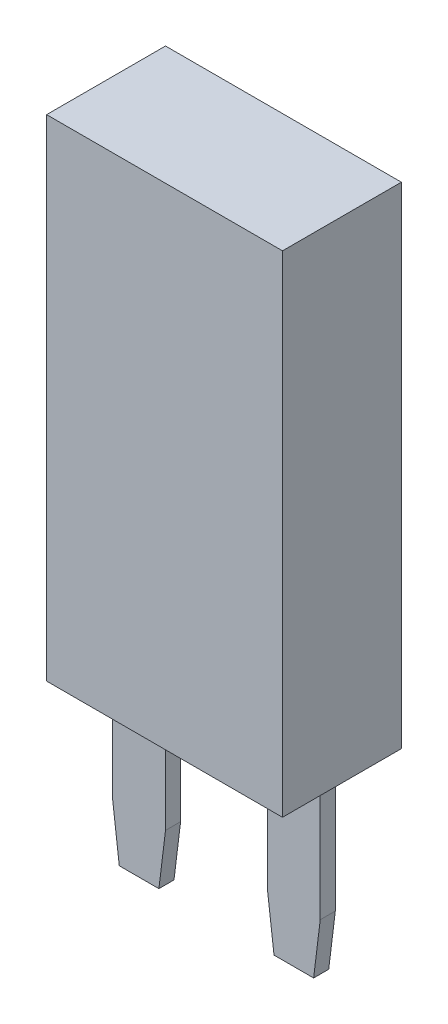
SolidWorks part; units mm, degrees
ref_plane "Front Plane" through (0, 0, 0) normal (0, 0, 1) x (1, 0, 0)
ref_plane "Top Plane" through (0, 0, 0) normal (0, 1, 0) x (1, 0, 0)
ref_plane "Right Plane" through (0, 0, 0) normal (1, 0, 0) x (0, 0, -1)
sketch "Sketch1" plane through (0, 0, 0) normal (0, 0, 1) x (1, 0, 0)
  line L1 (-6.25, 13) -> (6.25, 13)
  line L2 (-6.25, 13) -> (-6.25, -13)
  line L3 (-6.25, -13) -> (6.25, -13)
  line L4 (6.25, 13) -> (6.25, -13)
  line L5 (-6.25, 13) -> (6.25, -13) construction
  line L6 (-6.25, -13) -> (6.25, 13) construction
  point P0 (0, 0)
  dimension "D1" = 26
  dimension "D2" = 12.5
extrude "Boss-Extrude1" add sketch "Sketch1" along normal mid plane 6.3
sketch "Sketch2" plane through (0, -13, 0) normal (0, -1, 0) x (1, 0, 0)
  line L0 (0, 3.9068) -> (0, -3.8663) construction
  line L1 (2.7, 0.4) -> (2.7, -0.4)
  line L2 (-5.5, 0.4) -> (-2.7, 0.4)
  line L3 (-5.5, 0.4) -> (-5.5, -0.4)
  line L4 (-5.5, -0.4) -> (-2.7, -0.4)
  line L5 (-2.7, 0.4) -> (-2.7, -0.4)
  line L6 (5.5, -0.4) -> (2.7, -0.4)
  line L7 (5.5, 0.4) -> (5.5, -0.4)
  line L8 (5.5, 0.4) -> (2.7, 0.4)
  point P7 (-2.7, 0)
  dimension "D1" = 2.8
  dimension "D2" = 0.8
  dimension "D3" = 11
extrude "Boss-Extrude2" add sketch "Sketch2" along normal blind 9.3
chamfer "Chamfer1" distance 0.35 angle 83 4 edges at (5.5, -22.3, 0) (2.7, -22.3, 0) (-2.7, -22.3, 0) (-5.5, -22.3, 0)
